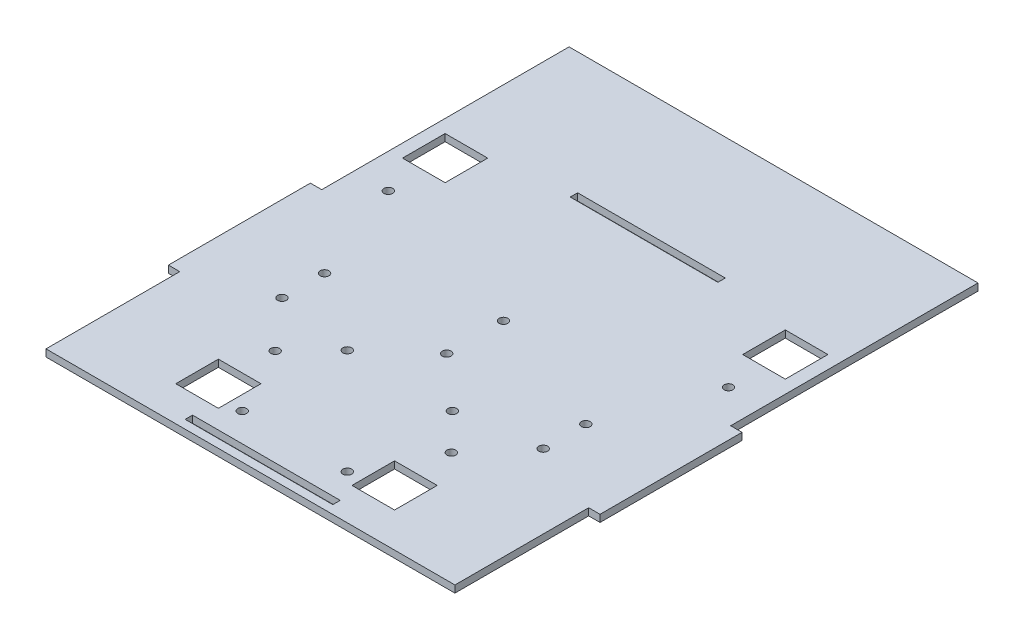
SolidWorks part; units mm, degrees
ref_plane "Front Plane" through (0, 0, 0) normal (0, 0, 1) x (1, 0, 0)
ref_plane "Top Plane" through (0, 0, 0) normal (0, 1, 0) x (1, 0, 0)
ref_plane "Right Plane" through (0, 0, 0) normal (1, 0, 0) x (0, 0, -1)
sketch "Sketch1" plane through (0, 0, 0) normal (0, 1, 0) x (1, 0, 0)
  line L5 (-72, -25) -> (-76, -25)
  line L7 (-72, 25) -> (-76, 25)
  line L21 (0, -78.079) -> (0, 78.079) construction
  line L22 (0, 0) -> (-74, 0) construction
  line L25 (72, -25) -> (76, -25)
  line L27 (72, 25) -> (76, 25)
  line L32 (67.3984, 63.8479) -> (52.3984, 63.8479)
  line L33 (-67.3984, 48.8479) -> (-52.3984, 48.8479)
  line L34 (-67.3984, 48.8479) -> (-67.3984, 63.8479)
  line L35 (-67.3984, 63.8479) -> (-52.3984, 63.8479)
  line L36 (-52.3984, 48.8479) -> (-52.3984, 63.8479)
  line L37 (52.3984, 48.8479) -> (52.3984, 63.8479)
  line L38 (67.3984, 48.8479) -> (52.3984, 48.8479)
  line L39 (67.3984, 48.8479) -> (67.3984, 63.8479)
  line L44 (38.5189, -44.8779) -> (38.5189, -59.8779)
  line L45 (23.5189, -44.8779) -> (23.5189, -59.8779)
  line L46 (23.5189, -59.8779) -> (38.5189, -59.8779)
  line L47 (23.5189, -44.8779) -> (38.5189, -44.8779)
  line L48 (-23.5189, -44.8779) -> (-38.5189, -44.8779)
  line L49 (-23.5189, -44.8779) -> (-23.5189, -59.8779)
  line L50 (-23.5189, -59.8779) -> (-38.5189, -59.8779)
  line L51 (-38.5189, -44.8779) -> (-38.5189, -59.8779)
  line L56 (-72, -72.1) -> (72, -72.1)
  line L57 (-26, -69.1) -> (26, -69.1)
  line L58 (-26, -69.1) -> (-26, -66.5)
  line L59 (-26, -66.5) -> (26, -66.5)
  line L60 (26, -69.1) -> (26, -66.5)
  line L63 (-26, 66.5) -> (26, 66.5)
  line L64 (26, 69.1) -> (26, 66.5)
  line L65 (-26, 69.1) -> (26, 69.1)
  line L66 (-26, 69.1) -> (-26, 66.5)
  line L67 (72, 25) -> (72, 72.1)
  line L68 (-72, 72.1) -> (72, 72.1)
  line L69 (-72, 25) -> (-72, 72.1)
  line L70 (-72, -25) -> (-72, -72.1)
  line L71 (72, -25) -> (72, -72.1)
  line L72 (-76, -25) -> (-76, 25)
  line L73 (76, -25) -> (76, 25)
  line L74 (31.0189, -32.3779) -> (31.0189, -52.3779) construction
  line L75 (-59.8984, 56.3479) -> (-59.8984, 36.3479) construction
  circle A0 centre (-18.5, -56.5) radius 1.55
  circle A1 centre (-18.5, -19.5) radius 1.55
  circle A2 centre (18.5, -19.5) radius 1.55
  circle A3 centre (18.5, -56.5) radius 1.55
  circle A4 centre (0, -3) radius 1.55
  circle A5 centre (0, 17) radius 1.55
  circle A6 centre (-59.8984, 36.3479) radius 1.55
  circle A7 centre (59.8984, 36.3479) radius 1.55
  circle A8 centre (31.0189, -32.3779) radius 1.55
  circle A9 centre (-31.0189, -32.3779) radius 1.55
  circle A10 centre (-46, -15) radius 1.55
  circle A11 centre (-46, 0) radius 1.55
  circle A12 centre (46, -15) radius 1.55
  circle A13 centre (46, 0) radius 1.55
  point P9 (0, 0)
  point P14 (0, -38)
  point P18 (0, -74)
  point P28 (-74, 0)
  point P30 (0, 69)
  point P33 (0, -25)
  point P40 (0, -38)
  point P41 (0, 43)
  point P45 (37.5, 0)
  point P47 (-37.5, 0)
  point P48 (0, 20.5)
  point P49 (0, -20.5)
  point P50 (0, 60.5)
  point P51 (-23, 43)
  point P52 (23, 43)
  point P53 (0, 25.5)
  point P55 (-59.8984, 56.3479)
  point P65 (59.8984, 56.3479)
  point P74 (33.0189, -25.3779)
  point P75 (39.7689, -40.8779)
  point P76 (26.2689, -40.8779)
  point P77 (33.0189, -52.3779)
  point P78 (33.0189, -56.3779)
  point P85 (-33.0189, -56.3779)
  point P86 (-33.0189, -52.3779)
  point P91 (-39.7689, -40.8779)
  point P92 (-26.2689, -40.8779)
  point P95 (-33.0189, -25.3779)
  point P97 (0, -67.8)
  dimension "D12" = 3.1
  dimension "D19" = 3.1
  dimension "D20" = 20
  dimension "D21" = 3.1
  dimension "D39" = 3.1
  dimension "D18" = 17
  dimension "D9" = 20
  dimension "D30" = 57.1
  dimension "D31" = 15
  dimension "D32" = 26
  dimension "D5" = 50
  dimension "D6" = 10
  dimension "D7" = 3
  dimension "D8" = 72.1
  dimension "D10" = 72
  dimension "D11" = 2.6
  dimension "D13" = 18.5
  dimension "D14" = 1.3
  dimension "D15" = 18.5
  dimension "D17" = 37
  dimension "D22" = 35
  dimension "D23" = 46
  dimension "D24" = 7.5
  dimension "D25" = 15
  dimension "D26" = 5
  dimension "D27" = 23
  dimension "D28" = 17.5
  dimension "D29" = 37.5
  dimension "D36" = 15
  dimension "D37" = 15
  dimension "D40" = 26
  dimension "D41" = 4
  dimension "D42" = 47.1
  dimension "D43" = 26
  dimension "D44" = 15
  dimension "D46" = 7.5
  dimension "D47" = 18.5
  dimension "D16" = 4
extrude "Boss-Extrude1" add sketch "Sketch1" along normal blind 2.5
sketch "Sketch2" plane through (0, 2.5, 0) normal (0, 1, 0) x (1, 0, 0)
  line L0 (-72, 72.1) -> (-72, 112.1)
  line L1 (-72, 112.1) -> (72, 112.1)
  line L2 (72, 112.1) -> (72, 72.1)
  line L12 (72, -25) -> (76, -25)
  line L13 (76, -25) -> (76, 25)
  line L14 (76, 25) -> (72, 25)
  line L15 (72, 25) -> (72, 72.1)
  line L16 (72, 72.1) -> (-72, 72.1)
  line L17 (-72, 72.1) -> (-72, 25)
  line L18 (-72, 25) -> (-76, 25)
  line L19 (-76, 25) -> (-76, -25)
  line L20 (-76, -25) -> (-72, -25)
  line L21 (-72, -25) -> (-72, -72.1)
  line L22 (-72, -72.1) -> (72, -72.1)
  line L23 (72, -72.1) -> (72, -25)
  line L24 (72, -25) -> (76, -25)
  line L25 (76, -25) -> (76, 25)
  line L26 (76, 25) -> (72, 25)
  line L27 (72, 25) -> (72, 72.1)
  line L28 (72, 72.1) -> (-72, 72.1)
  line L29 (-72, 72.1) -> (-72, 25)
  line L30 (-72, 25) -> (-76, 25)
  line L31 (-76, 25) -> (-76, -25)
  line L32 (-76, -25) -> (-72, -25)
  line L33 (-72, -25) -> (-72, -72.1)
  line L34 (-72, -72.1) -> (72, -72.1)
  line L35 (72, -72.1) -> (72, -25)
  line M51 (72, 72.1) -> (-72, 72.1)
  dimension "D2" = 40
  dimension "D1" = 0
extrude "Boss-Extrude2" add sketch "Sketch2" against normal blind 2.5 contours L2 L1 L0 M51
